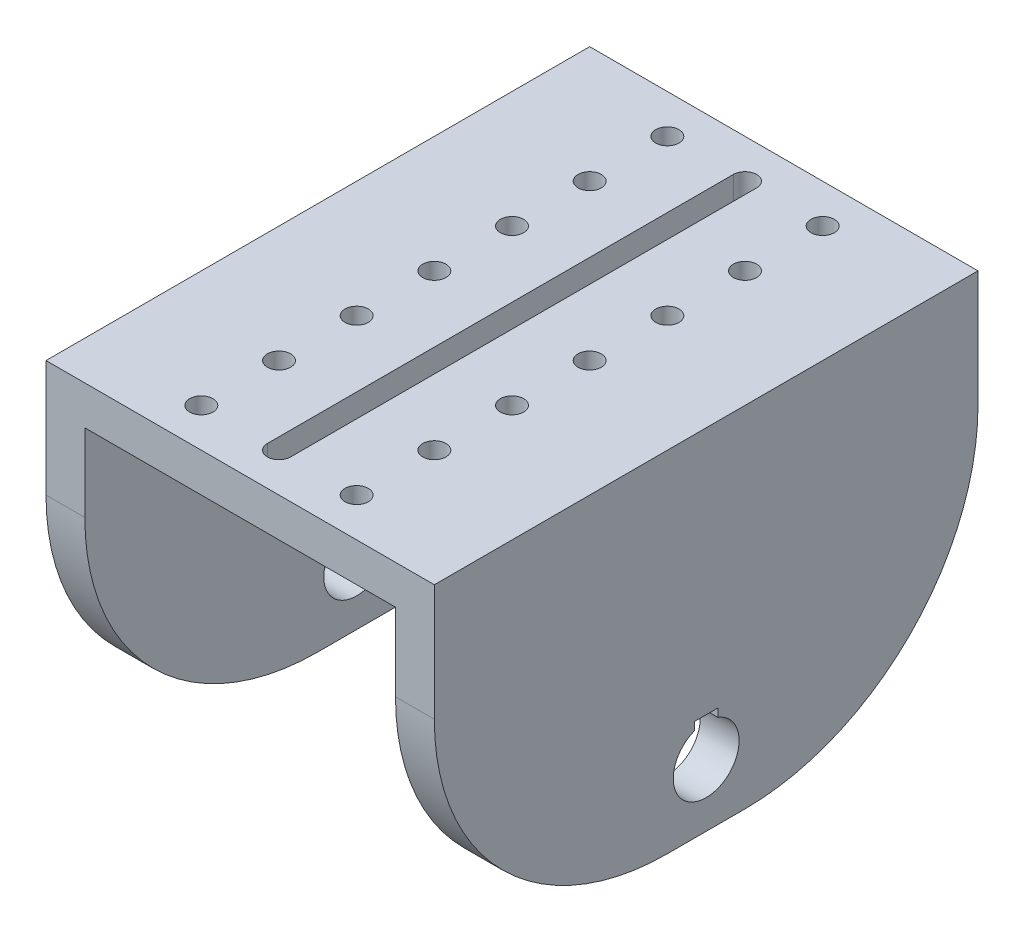
SolidWorks part; units mm, degrees
ref_plane "Front Plane" through (0, 0, 0) normal (0, 0, 1) x (1, 0, 0)
ref_plane "Top Plane" through (0, 0, 0) normal (0, 1, 0) x (1, 0, 0)
ref_plane "Right Plane" through (0, 0, 0) normal (1, 0, 0) x (0, 0, -1)
sketch "Sketch1" plane through (0, 0, 0) normal (0, 1, 0) x (1, 0, 0)
  line L0 (-197.2194, 124.9346) -> (-197.2194, 64.9346)
  line L1 (-220.7194, 129.9346) -> (-170.7194, 129.9346)
  line L2 (-220.7194, 129.9346) -> (-220.7194, 59.9346)
  line L3 (-220.7194, 59.9346) -> (-170.7194, 59.9346)
  line L4 (-170.7194, 129.9346) -> (-170.7194, 59.9346)
  line L5 (-194.2194, 124.9346) -> (-194.2194, 64.9346)
  circle A1 centre (-185.7194, 94.9346) radius 1.5
  circle A3 centre (-205.7194, 94.9346) radius 1.5
  circle A6 centre (-205.7194, 104.9346) radius 1.5
  circle A8 centre (-185.7194, 104.9346) radius 1.5
  circle A11 centre (-205.7194, 114.9346) radius 1.5
  circle A13 centre (-185.7194, 114.9346) radius 1.5
  circle A16 centre (-205.7194, 124.9346) radius 1.5
  arc A17 (-194.2194, 124.9346) -> (-197.2194, 124.9346) centre (-195.7194, 124.9346) ccw
  circle A18 centre (-185.7194, 124.9346) radius 1.5
  circle A21 centre (-205.7194, 84.9346) radius 1.5
  circle A23 centre (-185.7194, 84.9346) radius 1.5
  circle A26 centre (-205.7194, 74.9346) radius 1.5
  circle A28 centre (-185.7194, 74.9346) radius 1.5
  circle A31 centre (-205.7194, 64.9346) radius 1.5
  arc A32 (-197.2194, 64.9346) -> (-194.2194, 64.9346) centre (-195.7194, 64.9346) ccw
  circle A33 centre (-185.7194, 64.9346) radius 1.5
  dimension "D1" = 50
  dimension "D2" = 70
  dimension "D5" = 4
  dimension "D6" = 4
extrude "Boss-Extrude1" add sketch "Sketch1" along normal blind 5
sketch "Sketch2" plane through (0, 0, 0) normal (0, 1, 0) x (1, 0, 0)
  line L0 (-170.7194, 129.9346) -> (-220.7194, 129.9346) construction
  line L1 (-220.7194, 59.9346) -> (-215.7194, 59.9346)
  line L2 (-220.7194, 59.9346) -> (-220.7194, 129.9346)
  line L3 (-220.7194, 129.9346) -> (-215.7194, 129.9346)
  line L4 (-215.7194, 59.9346) -> (-215.7194, 129.9346)
  line L6 (-170.7194, 59.9346) -> (-175.7194, 59.9346)
  line L7 (-170.7194, 59.9346) -> (-170.7194, 129.9346)
  line L8 (-170.7194, 129.9346) -> (-175.7194, 129.9346)
  line L9 (-175.7194, 59.9346) -> (-175.7194, 129.9346)
  dimension "D1" = 5
  dimension "D2" = 5
extrude "Boss-Extrude2" add sketch "Sketch2" against normal blind 40
fillet "Fillet1" radius 30 4 edges at (-173.2194, -40, -59.9346) (-218.2194, -40, -59.9346) (-218.2194, -40, -129.9346) (-173.2194, -40, -129.9346)
sketch "Sketch3" plane through (-170.7194, 0, 0) normal (1, 0, 0) x (0, 0, -1)
  line L0 (89.9346, -40) -> (99.9346, -40) construction
  line L1 (94.9346, -32) -> (94.9346, -27) construction
  line L2 (94.9346, -27) -> (96.4346, -27)
  line L3 (96.4346, -27) -> (96.4346, -28.0342)
  line L4 (94.9346, -27) -> (93.4346, -27)
  line L5 (93.4346, -27) -> (93.4346, -28.0342)
  arc A0 (93.4346, -28.0342) -> (96.4346, -28.0342) centre (94.9346, -32) ccw
  dimension "D1" = 8
  dimension "D2" = 8.48
  dimension "D3" = 5
  dimension "D4" = 1.5
  dimension "D5" = 3
extrude "Cut-Extrude1" cut sketch "Sketch3" against normal through all
